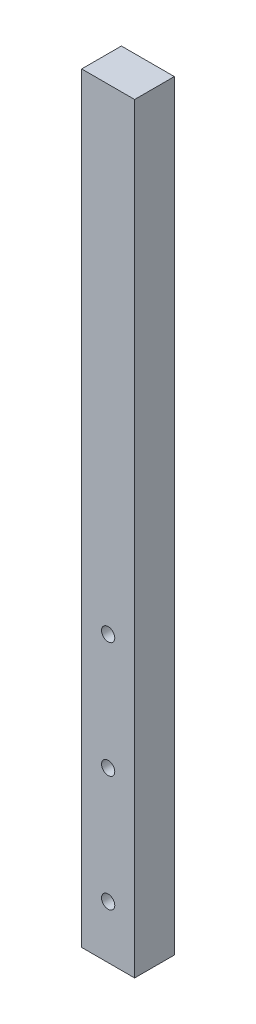
SolidWorks part; units mm, degrees
ref_plane "Front Plane" through (0, 0, 0) normal (0, 0, 1) x (1, 0, 0)
ref_plane "Top Plane" through (0, 0, 0) normal (0, 1, 0) x (1, 0, 0)
ref_plane "Right Plane" through (0, 0, 0) normal (1, 0, 0) x (0, 0, -1)
sketch "Model" plane through (0, 0, 0) normal (0, 0, 1) x (1, 0, 0)
  line L0 (33.1333, 122.0854) -> (33.1333, 7.0854)
  line L1 (33.1333, 7.0854) -> (41.1333, 7.0854)
  line L2 (41.1333, 7.0854) -> (41.1333, 122.0854)
  line L3 (33.1333, 122.0854) -> (41.1333, 122.0854)
  circle A0 centre (37.1333, 15.0854) radius 1
  circle A1 centre (37.1333, 50.0854) radius 1
  circle A2 centre (37.1333, 32.5854) radius 1
extrude "Boss-Extrude1" add sketch "Model" along normal blind 6 contours L2 L3 L0 L1 | A0 | A2 | A1
